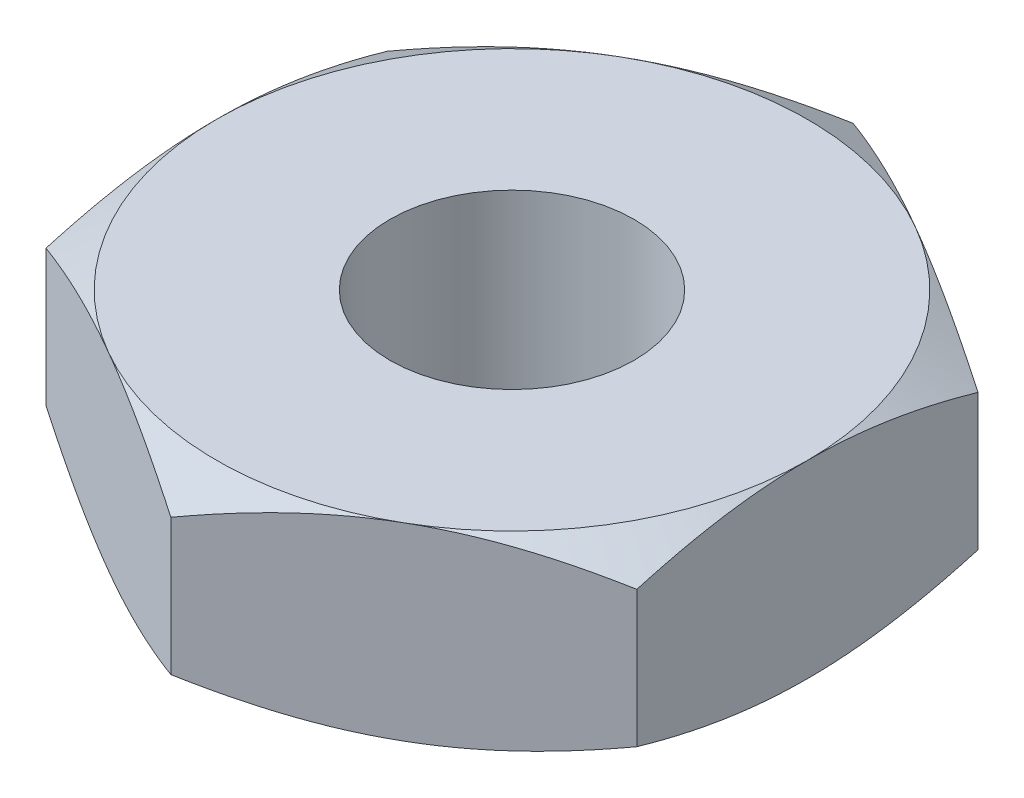
SolidWorks part; units mm, degrees
ref_plane "前视基准面" through (0, 0, 0) normal (0, 0, 1) x (1, 0, 0)
ref_plane "上视基准面" through (0, 0, 0) normal (0, 1, 0) x (1, 0, 0)
ref_plane "右视基准面" through (0, 0, 0) normal (1, 0, 0) x (0, 0, -1)
sketch "草图1" plane through (0, 0, 0) normal (0, 1, 0) x (1, 0, 0)
  line L0 (0, 0) -> (0, 2.8868) construction
  line L1 (0, 2.8868) -> (-2.5, 1.4434)
  line L2 (-2.5, 1.4434) -> (-2.5, -1.4434)
  line L3 (-2.5, -1.4434) -> (0, -2.8868)
  line L4 (0, -2.8868) -> (2.5, -1.4434)
  line L5 (2.5, -1.4434) -> (2.5, 1.4434)
  line L6 (2.5, 1.4434) -> (0, 2.8868)
  circle A0 centre (0, 0) radius 2.5 construction
  dimension "D1" = 5
extrude "凸台-拉伸1" add sketch "草图1" along normal blind 1.6
sketch "草图4" plane through (0, 1.6, 0) normal (0, 1, 0) x (1, 0, 0)
  circle A0 centre (0, 0) radius 1.0335
  dimension "D1" = 2.067
sketch "草图2" plane through (0, 0, 0) normal (1, 0, 0) x (0, 0, -1)
  line L0 (2.8868, 1.6) -> (2.8868, 1.3767)
  line L1 (2.8868, 1.6) -> (2.8868, 0) construction
  line L2 (2.8868, 1.3767) -> (2.5, 1.6)
  line L3 (1.4434, 1.6) -> (2.8868, 1.6) construction
  line L4 (2.5, 1.6) -> (2.8868, 1.6)
  line L5 (0, 0) -> (0, 2.0082) construction
  line L6 (-1.4434, 0) -> (1.4434, 0) construction
  dimension "D1" = 30
  dimension "D2" = 5
revolve "切除-旋转1" cut sketch "草图2" angle 360 about L5
sketch "草图3" plane through (0, 0, 0) normal (1, 0, 0) x (0, 0, -1)
  line L0 (2.8868, 0) -> (2.8868, 0.2233)
  line L1 (2.8868, 1.3767) -> (2.8868, 0) construction
  line L2 (2.8868, 0.2233) -> (2.5, 0)
  line L3 (1.4434, 0) -> (2.8868, 0) construction
  line L4 (2.5, 0) -> (2.8868, 0)
  line L5 (0, 0) -> (0, 2.0879) construction
  dimension "D1" = 30
  dimension "D2" = 5
revolve "切除-旋转2" cut sketch "草图3" angle 360 about L5
extrude "Cut-Extrude1" cut sketch "草图4" against normal blind 10
